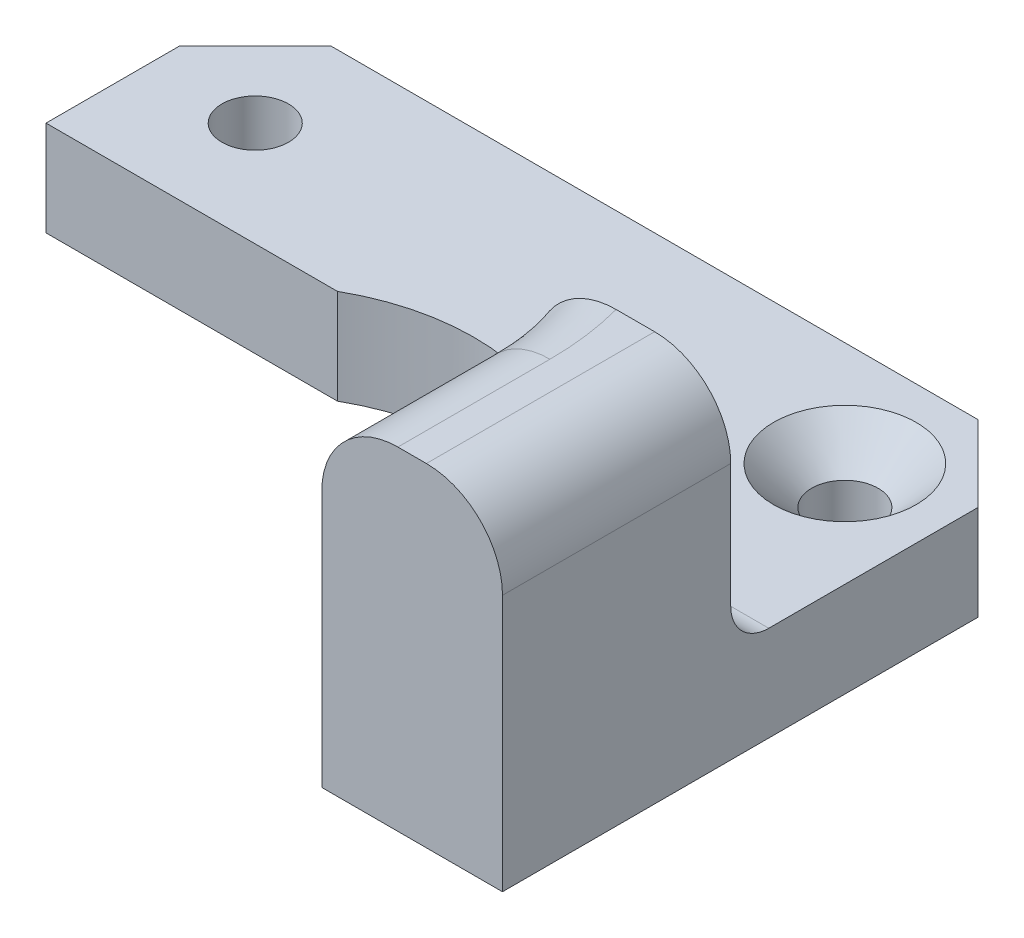
SolidWorks part; units mm, degrees
ref_plane "Alzado" through (0, 0, 0) normal (0, 0, 1) x (1, 0, 0)
ref_plane "Planta" through (0, 0, 0) normal (0, 1, 0) x (1, 0, 0)
ref_plane "Vista lateral" through (0, 0, 0) normal (1, 0, 0) x (0, 0, -1)
sketch "Croquis1" plane through (0, 0, 0) normal (0, 1, 0) x (1, 0, 0)
  line L0 (0, 23.3508) -> (0, -18.5531) construction
  line L1 (0, -9.7499) -> (0, 9.7499) construction
  line L2 (-9.7499, 0) -> (9.7499, 0) construction
  line L3 (-21, 21) -> (21, 21)
  line L4 (21, 21) -> (21, -8)
  line L5 (21, -8) -> (11.5, -8)
  line L6 (-21, 21) -> (-21, 10)
  line L7 (-21, 10) -> (-5.6789, 10)
  line L8 (11.5, 0) -> (11.5, -8)
  arc A0 (11.5, 0) -> (-5.6789, 10) centre (0, 0) ccw
  circle A1 centre (-15.5, 15.5) radius 1.5 construction
  circle A2 centre (15.5, 15.5) radius 1.5 construction
  circle A3 centre (-15.5, 15.5) radius 1.75
  circle A4 centre (15.5, 15.5) radius 1.75
  dimension "D1" = 23
  dimension "D2" = 3
  dimension "D7" = 3.5
  dimension "D3" = 15.5
  dimension "D4" = 31
  dimension "D5" = 42
  dimension "D6" = 21
  dimension "D8" = 10
  dimension "D9" = 8
extrude "Saliente-Extruir1" add sketch "Croquis1" along normal blind 5
chamfer "Chaflán1" distance 2 distance2 2 1 edges at (15.5, 5, -13.75)
sketch "Croquis3" plane through (0, 0, 0) normal (0, -1, 0) x (1, 0, 0)
  line L0 (10.7819, -4) -> (21, -4)
  line L1 (21, 8) -> (11.5, 8)
  line L2 (21, 8) -> (21, 0)
  line L3 (2.75, 0) -> (-2.75, 0) construction
  line L4 (11.5, 8) -> (11.5, 0)
  line L5 (21, 8) -> (21, -21) construction
  line L6 (11.5, 8) -> (21, 8) construction
  line L7 (11.5, 0) -> (11.5, 8) construction
  line L8 (21, -4) -> (21, 0)
  arc A0 (-5.6789, -10) -> (11.5, 0) centre (0, 0) ccw construction
  arc A1 (10.7819, -4) -> (11.5, 0) centre (0, 0) ccw
  dimension "D1" = 4
  dimension "D2" = 8
extrude "Saliente-Extruir2" add sketch "Croquis3" against normal blind 17.5
sketch "Croquis4" plane through (0, 0, -4) normal (0, 0, -1) x (-1, 0, 0)
  line L0 (-21, 12) -> (-11.5, 12) construction
  line L1 (-21, 17.5) -> (-21, 5) construction
  line L3 (-16.25, 17.5) -> (-16.25, 5) construction
  line L8 (15.95, 0) -> (-15.95, 0) construction
  circle A0 centre (-16.25, 12) radius 2.5
  dimension "D1" = 5
  dimension "D2" = 12
  dimension "D3" = 4.75
extrude "Saliente-Extruir3" add sketch "Croquis4" along normal blind 3
draft "Ángulo de salida1" type of draft neutral plane draft angle 20 faces to draft 1 face at (13.75, 12, -7) neutral plane through (10.7819, 17.5, -4) neutral plane normal (0, 0, -1) parameters "D1"=20
fillet "Redondeo1" radius 1 2 edges at (14.8419, 12, -7) (13.75, 12, -4)
chamfer "Chaflán2" distance 4 angle 45 2 edges at (-21, 2.5, -21) (21, 2.5, -21)
fillet "Redondeo2" radius 2 1 edges at (15.891, 5, -4)
fillet "Redondeo4" radius 4 3 edges at (21, 17.5, 2) (11.5, 17.5, 4) (11.3191, 17.5, -2.032)
